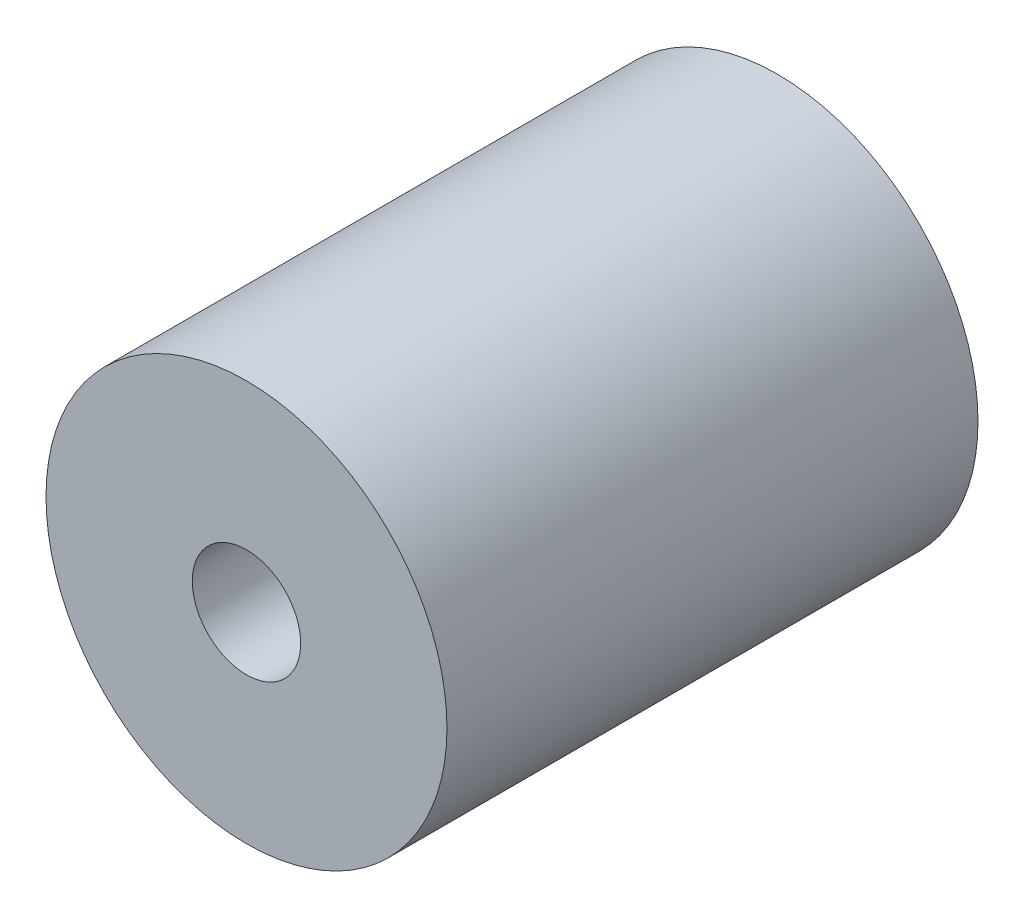
SolidWorks part; units mm, degrees
ref_plane "Front Plane" through (0, 0, 0) normal (0, 0, 1) x (1, 0, 0)
ref_plane "Top Plane" through (0, 0, 0) normal (0, 1, 0) x (1, 0, 0)
ref_plane "Right Plane" through (0, 0, 0) normal (1, 0, 0) x (0, 0, -1)
sketch "Sketch1" plane through (0, 0, 0) normal (0, 0, 1) x (1, 0, 0)
  circle A0 centre (0, 0) radius 9.398
  dimension "D1" = 18.796
extrude "Boss-Extrude1" add sketch "Sketch1" along normal blind 24.892
sketch "Sketch2" plane through (0, 0, 0) normal (0, 0, -1) x (-1, 0, 0)
  circle A0 centre (0, 0) radius 2.54
  dimension "D1" = 5.08
extrude "Cut-Extrude1" cut sketch "Sketch2" against normal through all both and the other way through all
sketch "Sketch3" plane through (0, 0, 0) normal (0, 0, -1) x (-1, 0, 0)
  circle A0 centre (0, 0) radius 3.9878
  dimension "D1" = 7.9756
extrude "Cut-Extrude2" cut sketch "Sketch3" against normal blind 12.446
